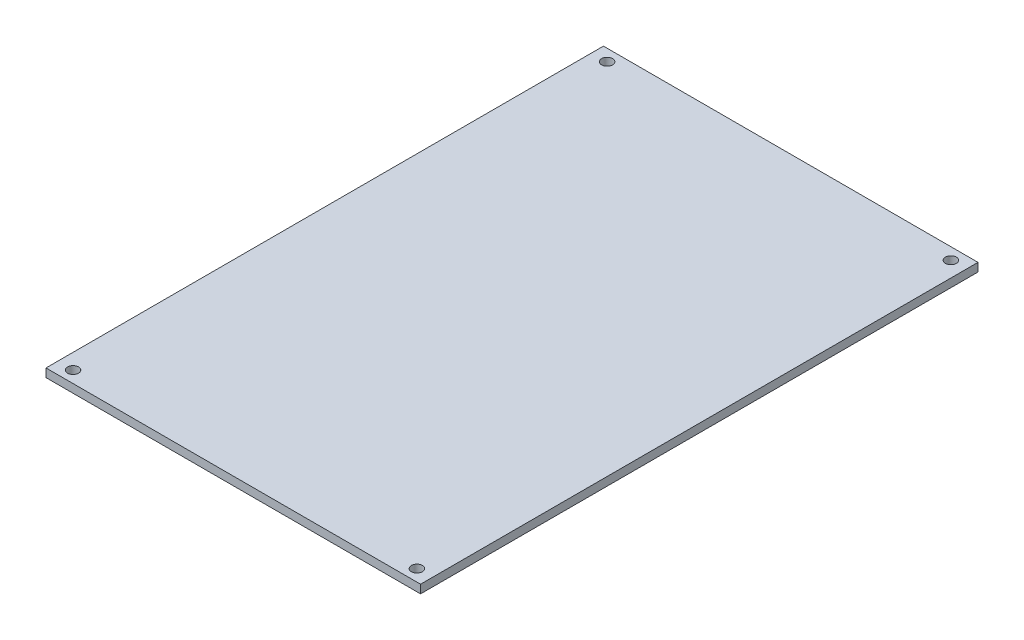
SolidWorks part; units mm, degrees
ref_plane "前基準面" through (0, 0, 0) normal (0, 0, 1) x (1, 0, 0)
ref_plane "上基準面" through (0, 0, 0) normal (0, 1, 0) x (1, 0, 0)
ref_plane "右基準面" through (0, 0, 0) normal (1, 0, 0) x (0, 0, -1)
sketch "草圖1" plane through (0, 0, 0) normal (0, 1, 0) x (1, 0, 0)
  line L1 (-51.2, -76.2) -> (51.2, -76.2)
  line L2 (-51.2, -76.2) -> (-51.2, 76.2)
  line L3 (-51.2, 76.2) -> (51.2, 76.2)
  line L4 (51.2, -76.2) -> (51.2, 76.2)
  line L5 (0, 76.2) -> (0, -76.2) construction
  line L6 (-51.2, 0) -> (51.2, 0) construction
  point P0 (0, 0)
  dimension "D1" = 102.4
  dimension "D2" = 152.4
extrude "填料-伸長1" add sketch "草圖1" along normal blind 2.3
sketch "草圖2" plane through (0, 2.3, 0) normal (0, 1, 0) x (1, 0, 0)
  line L0 (0, 87.524) -> (0, -87.524) construction
  line L1 (-67.5631, 0) -> (67.5631, 0) construction
  circle A0 centre (35.5, 0) radius 1.6
  circle A1 centre (-35.5, 0) radius 1.6
  circle A2 centre (35.5, -71) radius 1.6
  circle A3 centre (-35.5, -71) radius 1.6
  point P4 (0, 0)
  point P15 (0, 0)
  dimension "D1" = 3.2
  dimension "D2" = 71
  dimension "D3" = 71
extrude "除料-伸長1" [suppressed] cut sketch "草圖2" against normal through all
sketch "草圖3" plane through (0, 2.3, 0) normal (0, 1, 0) x (1, 0, 0)
  line L0 (0, 80.1988) -> (0, -109.7485) construction
  line L1 (-32.4805, -55.5425) -> (-32.4805, -64.5425)
  line L2 (30.1805, -55.5425) -> (32.4805, -55.5425)
  line L3 (30.1805, -55.5425) -> (30.1805, -64.5425)
  line L4 (30.1805, -64.5425) -> (32.4805, -64.5425)
  line L5 (32.4805, -55.5425) -> (32.4805, -64.5425)
  line L6 (-30.1805, -64.5425) -> (-32.4805, -64.5425)
  line L7 (-30.1805, -55.5425) -> (-30.1805, -64.5425)
  line L8 (-30.1805, -55.5425) -> (-32.4805, -55.5425)
  line L9 (-32.4805, -6.5425) -> (-32.4805, -15.5425)
  line L10 (30.1805, -6.5425) -> (32.4805, -6.5425)
  line L11 (30.1805, -6.5425) -> (30.1805, -15.5425)
  line L12 (30.1805, -15.5425) -> (32.4805, -15.5425)
  line L13 (32.4805, -6.5425) -> (32.4805, -15.5425)
  line L14 (-30.1805, -15.5425) -> (-32.4805, -15.5425)
  line L15 (-30.1805, -6.5425) -> (-30.1805, -15.5425)
  line L16 (-30.1805, -6.5425) -> (-32.4805, -6.5425)
  line L17 (10.1805, -55.5425) -> (10.1805, -64.5425)
  line L18 (-12.4805, -55.5425) -> (-10.1805, -55.5425)
  line L19 (-12.4805, -55.5425) -> (-12.4805, -64.5425)
  line L20 (-12.4805, -64.5425) -> (-10.1805, -64.5425)
  line L21 (-10.1805, -55.5425) -> (-10.1805, -64.5425)
  line L22 (12.4805, -64.5425) -> (10.1805, -64.5425)
  line L23 (12.4805, -55.5425) -> (12.4805, -64.5425)
  line L24 (12.4805, -55.5425) -> (10.1805, -55.5425)
  line L25 (10.1805, -6.5425) -> (10.1805, -15.5425)
  line L26 (-12.4805, -6.5425) -> (-10.1805, -6.5425)
  line L27 (-12.4805, -6.5425) -> (-12.4805, -15.5425)
  line L28 (-12.4805, -15.5425) -> (-10.1805, -15.5425)
  line L29 (-10.1805, -6.5425) -> (-10.1805, -15.5425)
  line L30 (12.4805, -15.5425) -> (10.1805, -15.5425)
  line L31 (12.4805, -6.5425) -> (12.4805, -15.5425)
  line L32 (12.4805, -6.5425) -> (10.1805, -6.5425)
  point P4 (0, 0)
  dimension "D1" = 2
  dimension "D2" = 2.3
  dimension "D3" = 9
  dimension "D4" = 2
  dimension "D5" = 40
  dimension "D6" = 20
extrude "除料-伸長2" [suppressed] cut sketch "草圖3" against normal through all
sketch "草圖4" plane through (0, 2.3, 0) normal (0, 1, 0) x (1, 0, 0)
  line L0 (-78.1702, 0) -> (78.1702, 0) construction
  line L1 (0, 81.2607) -> (0, -81.2607) construction
  circle A0 centre (-47, 73) radius 1.5
  circle A1 centre (47, 73) radius 1.5
  circle A2 centre (47, -73) radius 1.5
  circle A3 centre (-47, -73) radius 1.5
  point P4 (0, 0)
  point P7 (0, 0)
  dimension "D1" = 146
  dimension "D3" = 3
  dimension "D2" = 94
extrude "除料-伸長3" cut sketch "草圖4" against normal through all
